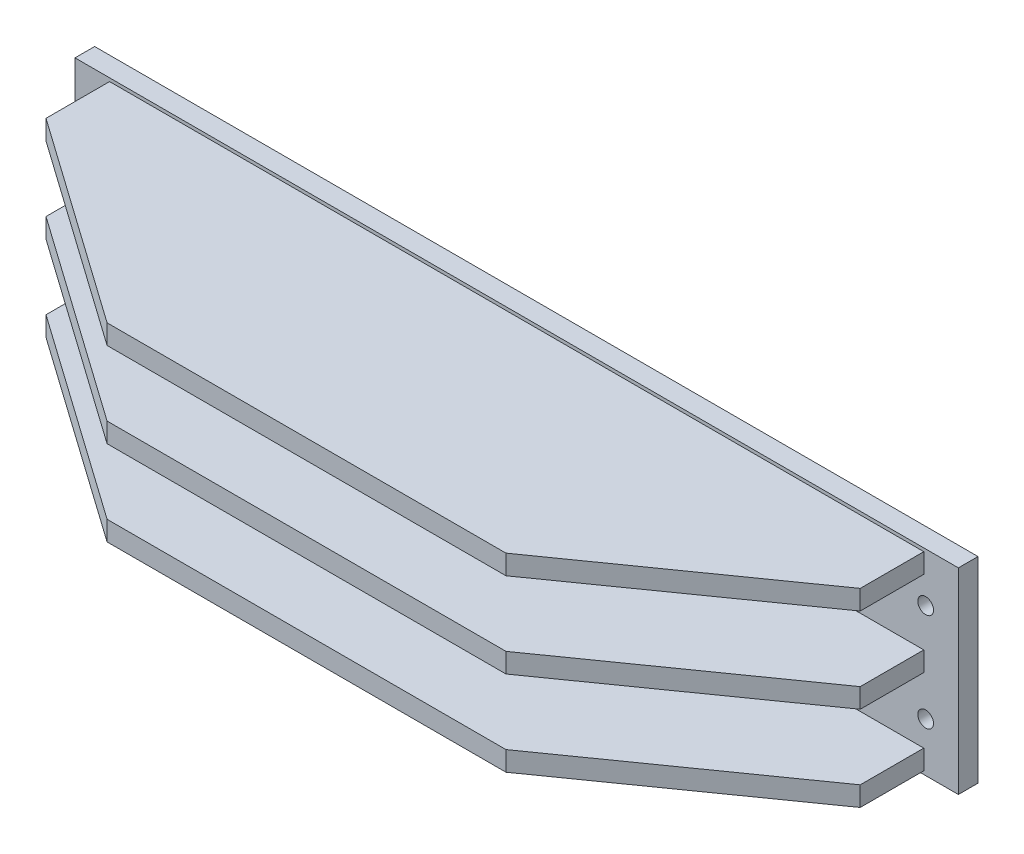
SolidWorks part; units mm, degrees
ref_plane "Front Plane" through (0, 0, 0) normal (0, 0, 1) x (1, 0, 0)
ref_plane "Top Plane" through (0, 0, 0) normal (0, 1, 0) x (1, 0, 0)
ref_plane "Right Plane" through (0, 0, 0) normal (1, 0, 0) x (0, 0, -1)
sketch "Sketch1" plane through (0, 0, 0) normal (0, 0, 1) x (1, 0, 0)
  line L0 (50.3393, -50.5544) -> (50.3393, 429.2458) construction
  line L1 (50.3393, -50.5544) -> (615.489, -50.5544) construction
  line L2 (725.3393, -200.5544) -> (725.3393, 99.4456)
  line L3 (725.3393, 99.4456) -> (-624.6607, 99.4456)
  line L4 (725.3393, -200.5544) -> (-624.6607, -200.5544)
  line L5 (-624.6607, -200.5544) -> (-624.6607, 99.4456)
  point P9 (725.3393, -50.5544)
  point P10 (50.3393, -200.5544)
  point P11 (50.3393, 99.4456)
  dimension "D1" = 150
  dimension "D2" = 675
extrude "Extrude1" add sketch "Sketch1" along normal blind 30
sketch "Sketch2" plane through (0, 0, 30) normal (0, 0, 1) x (1, 0, 0)
  line L0 (50.3393, -50.5544) -> (50.3393, 420.1598) construction
  line L1 (725.3393, -50.5544) -> (-651.1006, -50.5544) construction
  line L2 (725.3393, -200.5544) -> (725.3393, 99.4456) construction
  circle A0 centre (675.3393, 24.4456) radius 12
  circle A1 centre (675.3393, -125.5544) radius 12
  circle A2 centre (-574.6607, -125.5544) radius 12
  circle A3 centre (-574.6607, 24.4456) radius 12
  dimension "D5" = 24
  dimension "D6" = 24
  dimension "D1" = 75
  dimension "D2" = 75
  dimension "D3" = 625
  dimension "D4" = 625
extrude "Cut-Extrude1" cut sketch "Sketch2" against normal through all
ref_plane "Plane1" through (-624.6607, -50.5544, 0) normal (0, -1, 0) x (1, 0, 0)
sketch "Sketch3" plane through (-624.6607, -50.5544, 0) normal (0, -1, 0) x (1, 0, 0)
  line L0 (52.8349, 30) -> (52.8349, 127.1673)
  line L1 (0, 30) -> (1350, 30) construction
  line L2 (52.8349, 127.1673) -> (370.2, 351.19)
  line L3 (370.2, 545.2) -> (370.2, -1547.6) construction
  line L4 (370.2, 351.19) -> (979.8, 351.19)
  line L5 (675, -1547.6) -> (675, 850) construction
  line L6 (675, -102.8294) -> (675, 443.786) construction
  line L7 (1297.1651, 30) -> (1297.1651, 127.1673)
  line L8 (1297.1651, 127.1673) -> (979.8, 351.19)
  line L9 (1297.1651, 30) -> (52.8349, 30)
  point P13 (675, 351.19)
extrude "Extrude2" add sketch "Sketch3" along normal blind 15 and the other way blind 15
pattern_linear "LPattern1" count 2 spacing 130 along (0, -1, 0) count 2 spacing 130 along (0, 1, 0) of "Extrude2"
